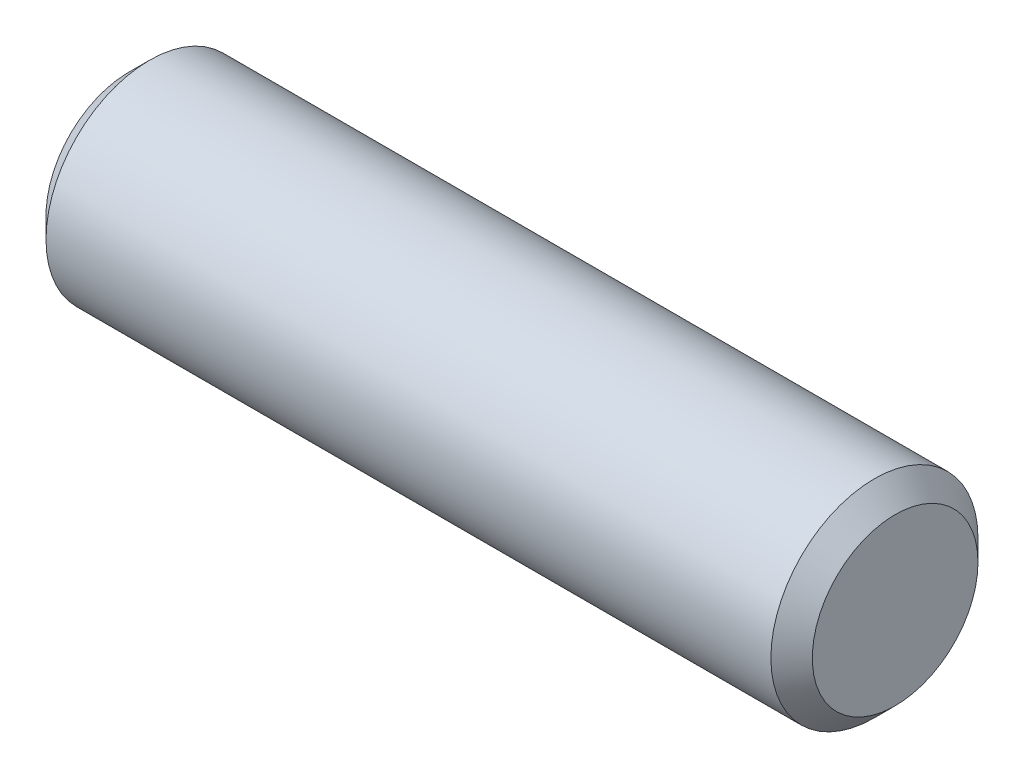
SolidWorks part; units mm, degrees
ref_plane "Front Plane" through (0, 0, 0) normal (0, 0, 1) x (1, 0, 0)
ref_plane "Top Plane" through (0, 0, 0) normal (0, 1, 0) x (1, 0, 0)
ref_plane "Right Plane" through (0, 0, 0) normal (1, 0, 0) x (0, 0, -1)
sketch "Sketch1" plane through (0, 0, 0) normal (1, 0, 0) x (0, 0, -1)
  circle A0 centre (0, 0) radius 10
  dimension "D1" = 20
extrude "Boss-Extrude1" add sketch "Sketch1" along normal blind 74
chamfer "Chamfer1" distance 2 angle 45 2 edges at (0, 0, -10) (74, 0, -10)
cosmetic thread "Cosmetic Thread1" parameters "D1"=24, "D2"=17.252
cosmetic thread "Cosmetic Thread2" parameters "D1"=24, "D2"=17.252
